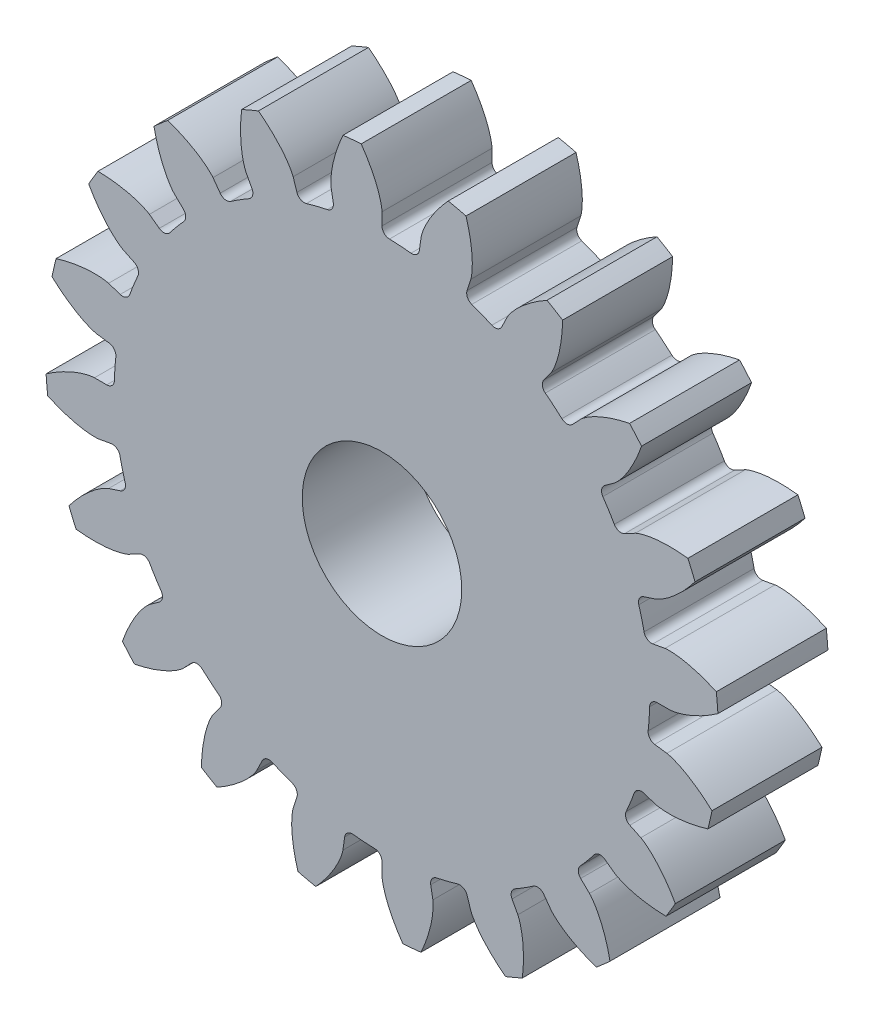
SolidWorks part; units mm, degrees
ref_plane "Front Plane" through (0, 0, 0) normal (0, 0, 1) x (1, 0, 0)
ref_plane "Top Plane" through (0, 0, 0) normal (0, 1, 0) x (1, 0, 0)
ref_plane "Right Plane" through (0, 0, 0) normal (1, 0, 0) x (0, 0, -1)
sketch "Sketch1" plane through (0, 0, 0) normal (0, 0, 1) x (1, 0, 0)
  line L0 (10.4541, 0) -> (9.7344, 0)
  line L1 (12.1891, 1.0871) -> (-12.1891, -1.0871)
  line L2 (0, 0) -> (11.1238, 0.1658) construction
  circle A0 centre (0, 0) radius 10.4541 construction
  circle A1 centre (0, 0) radius 12.2375
  circle A2 centre (0, 0) radius 9.7344
  circle A3 centre (0, 0) radius 11.125 construction
  spline S0 degree 4 poles (10.4541, 0) (10.4618, 0.0002) (10.4835, 0.0011) (10.5243, 0.005) (10.5907, 0.014) (10.6748, 0.0297) (10.7827, 0.0547) (10.9086, 0.0902) (11.0454, 0.1354) (11.1924, 0.1913) (11.3372, 0.2529) (11.4797, 0.3198) (11.6199, 0.3911) (11.7874, 0.4832) (11.9848, 0.6012) (12.2103, 0.7502) (12.4593, 0.9319) (12.7053, 1.1303) (12.9407, 1.3362) (13.1705, 1.5561) (13.387, 1.7772) (13.6028, 2.0184) (13.7974, 2.2469) (14.0048, 2.5149) (14.1692, 2.7349) (14.3742, 3.0372) (14.4917, 3.2193) (14.625, 3.4365) (14.682, 3.5351) (14.7171, 3.5957) knots 0 0 0 0 0 0.005377 0.015084 0.028532 0.04661 0.064855 0.092111 0.119476 0.146842 0.174209 0.201575 0.228941 0.256307 0.307035 0.361767 0.4165 0.471232 0.525964 0.580697 0.635429 0.690161 0.744894 0.799626 0.854358 0.909091 0.954545 1 1 1 1 1 construction
  spline S1 degree 4 poles (10.4541, 0) (10.4618, 0.0002) (10.4835, 0.0011) (10.5243, 0.005) (10.5907, 0.014) (10.6748, 0.0297) (10.7827, 0.0547) (10.9086, 0.0902) (11.0454, 0.1354) (11.1924, 0.1913) (11.3372, 0.2529) (11.4797, 0.3198) (11.6199, 0.3911) (11.7874, 0.4832) (11.9848, 0.6012) (12.2103, 0.7502) (12.4593, 0.9319) (12.7053, 1.1303) (12.9407, 1.3362) (13.1705, 1.5561) (13.387, 1.7772) (13.6028, 2.0184) (13.7974, 2.2469) (14.0048, 2.5149) (14.1692, 2.7349) (14.3298, 2.9716) (14.4065, 3.0883) (14.4452, 3.1484) knots 0 0 0 0 0 0.005377 0.015084 0.028532 0.04661 0.064855 0.092111 0.119476 0.146842 0.174209 0.201575 0.228941 0.256307 0.307035 0.361767 0.4165 0.471232 0.525964 0.580697 0.635429 0.690161 0.744894 0.799626 0.854358 0.909091 0.909091 0.909091 0.909091 0.909091
  dimension "D1" = 20.9082
  dimension "D2" = 24.475
  dimension "D3" = 19.4688
  dimension "D5" = 22.25
  dimension "D4" = 4.242
extrude "Boss-Extrude3" add sketch "Sketch1" along normal blind 4 contours L1 A2 | A2 L1 | L0 S1 A1 L1 A2
mirror "Mirror2" about plane through (0, 0, 4) normal (0.0888, -0.996, 0) of "Boss-Extrude3"
fillet "Fillet1" radius 0.2781 2 edges at (9.5807, 1.7226, 2) (9.7344, 0, 2)
pattern_circular "CirPattern8" count 20 over 360 about axis through (0, 0, 4) along (0, 0, -1) of "Boss-Extrude3", "Mirror2", "Fillet1"
sketch "Sketch3" plane through (0, 0, 4) normal (0, 0, 1) x (1, 0, 0)
  circle A0 centre (0, 0) radius 2.9
  dimension "D1" = 5.8
extrude "Cut-Extrude2" cut sketch "Sketch3" against normal through all
equation "\"d\"= 22.25mm'Pitch diameter"
equation "\"N\"= 20'Number of teeth"
equation "\"bl\"= 0.1mm'Backlash"
equation "\"pa\"= 20deg'Pressure angle (deg)"
equation "\"pc\"= ( 3.1415 * \"d\" ) / \"N\"\t'Circular pitch"
equation "\"m\"= \"d\" / \"N\"\t\t\t'module"
equation "\"P\"= \"N\" / \"d\"\t\t\t'Diametral pitch"
equation "\"a\"= 1/\"P\"\t\t\t'Addendum distance"
equation "\"b\"= 1.25 / \"P\"'Dedendum distance"
equation "\"rb\"= (\"d\"/2)*cos(\"pa\")\t\t'base circle radius"
equation "\"cp\"= 3.1415/\"P\"\t\t'Circular pitch"
equation "\"t\"= ( \"cp\" / 2 ) - \"bl\"'tooth tickness"
equation "\"c\"=\"b\"-\"a\"\t\t\t'Clearance"
equation "\"facewidth\"= 4'face width"
equation "\"rbd\"= \"rb\" * 2'base circle diameter"
equation "\"D1@Sketch1\"=\"rbd\""
equation "\"D2@Sketch1\"= \"d\" + (\"a\" * 2)"
equation "\"D3@Sketch1\" = \"ded\""
equation "\"D4@Sketch1\"= ((\"t\" /2) / (\"d\"/2)) * (180/3.1415)"
equation "\"D1@Boss-Extrude3\"=\"facewidth\""
equation "\"D1@Fillet1\"=\"c\""
equation "\"D1@CirPattern8\"=\"N\""
equation "\"D5@Sketch1\"=\"d\""
equation "\"ded1\"= \"d\" - 2 * ( ( ( \"d\" / 2 ) - \"rb\" ) + ( 0.5 * ( 1.25 / \"P\" ) ) )"
equation "\"ded2\"= \"d\" - ( \"b\" * 2 )"
equation "\"ded\"= IIF ( \"rb\" < ( \"ded2\" / 2 ) , \"ded1\" , \"ded2\" )"
equation "\"shaftdia\"= 5.8"
equation "\"D1@Sketch3\"=\"shaftdia\""
